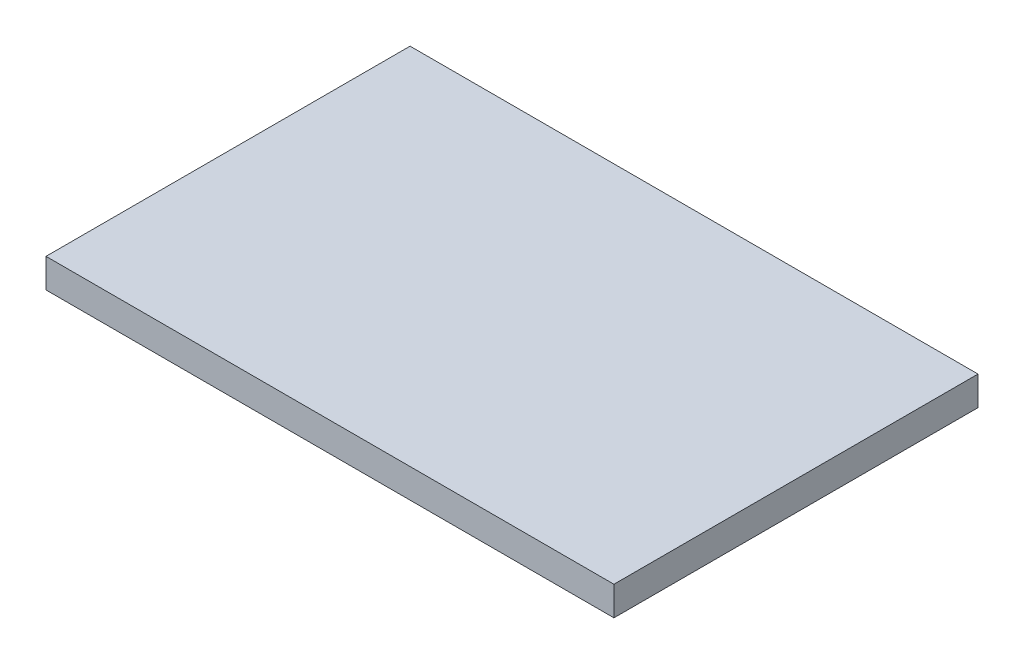
SolidWorks part; units mm, degrees
ref_plane "Front Plane" through (0, 0, 0) normal (0, 0, 1) x (1, 0, 0)
ref_plane "Top Plane" through (0, 0, 0) normal (0, 1, 0) x (1, 0, 0)
ref_plane "Right Plane" through (0, 0, 0) normal (1, 0, 0) x (0, 0, -1)
sketch "Sketch1" plane through (0, 0, 0) normal (0, 1, 0) x (1, 0, 0)
  line L1 (-39, -25) -> (39, -25)
  line L2 (-39, -25) -> (-39, 25)
  line L3 (-39, 25) -> (39, 25)
  line L4 (39, -25) -> (39, 25)
  line L5 (-39, -25) -> (39, 25) construction
  line L6 (-39, 25) -> (39, -25) construction
  point P0 (0, 0)
  dimension "D1" = 78
  dimension "D2" = 50
extrude "Boss-Extrude1" add sketch "Sketch1" along normal blind 4
